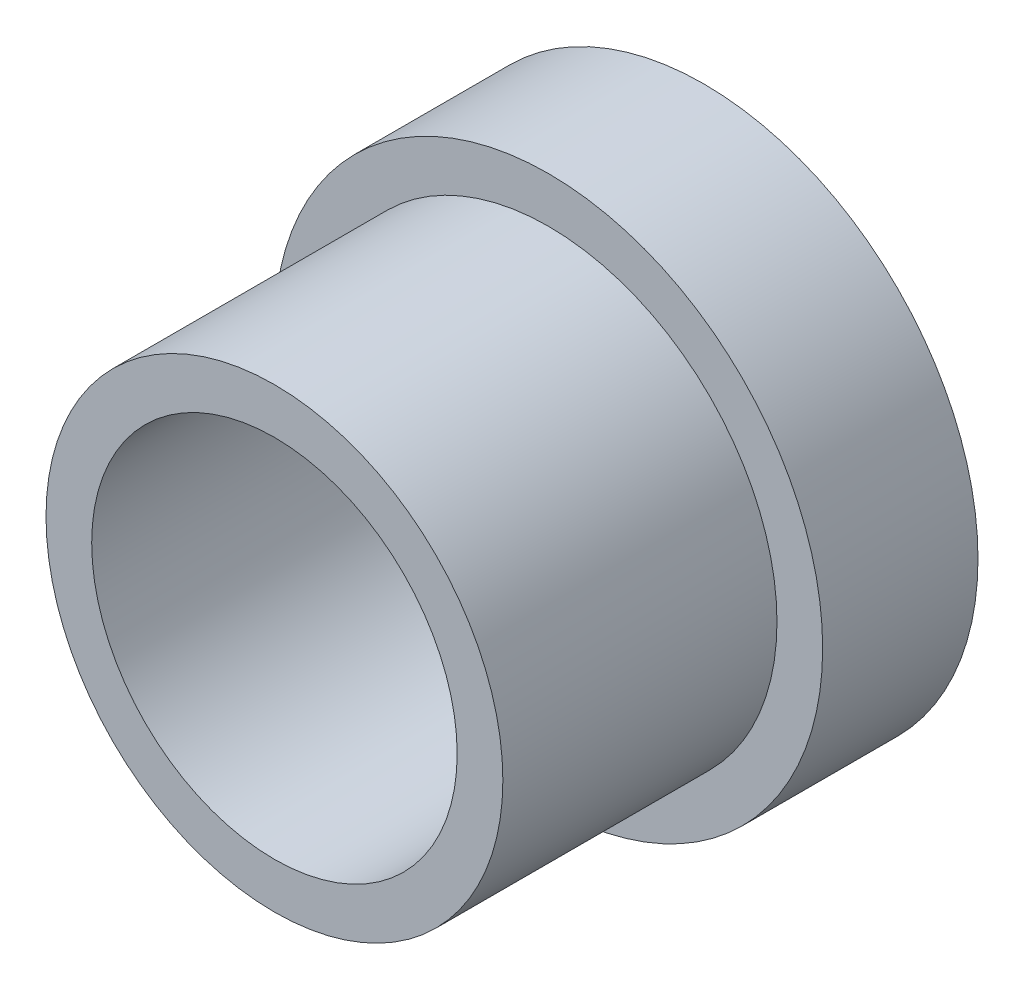
SolidWorks part; units mm, degrees
material "Tin Bearing Bronze"
ref_plane "Front Plane" through (0, 0, 0) normal (0, 0, 1) x (1, 0, 0)
ref_plane "Top Plane" through (0, 0, 0) normal (0, 1, 0) x (1, 0, 0)
ref_plane "Right Plane" through (0, 0, 0) normal (1, 0, 0) x (0, 0, -1)
sketch "Sketch1" plane through (0, 0, 0) normal (0, 0, 1) x (1, 0, 0)
  circle A0 centre (0, 0) radius 3
  circle A1 centre (0, 0) radius 2
extrude "Boss-Extrude1" add sketch "Sketch1" along normal blind 1.7
sketch "Sketch3" plane through (0, 0, 1.7) normal (0, 0, 1) x (1, 0, 0)
  circle A0 centre (0, 0) radius 2
  circle A1 centre (0, 0) radius 2.5
extrude "Boss-Extrude2" add sketch "Sketch3" along normal blind 3
